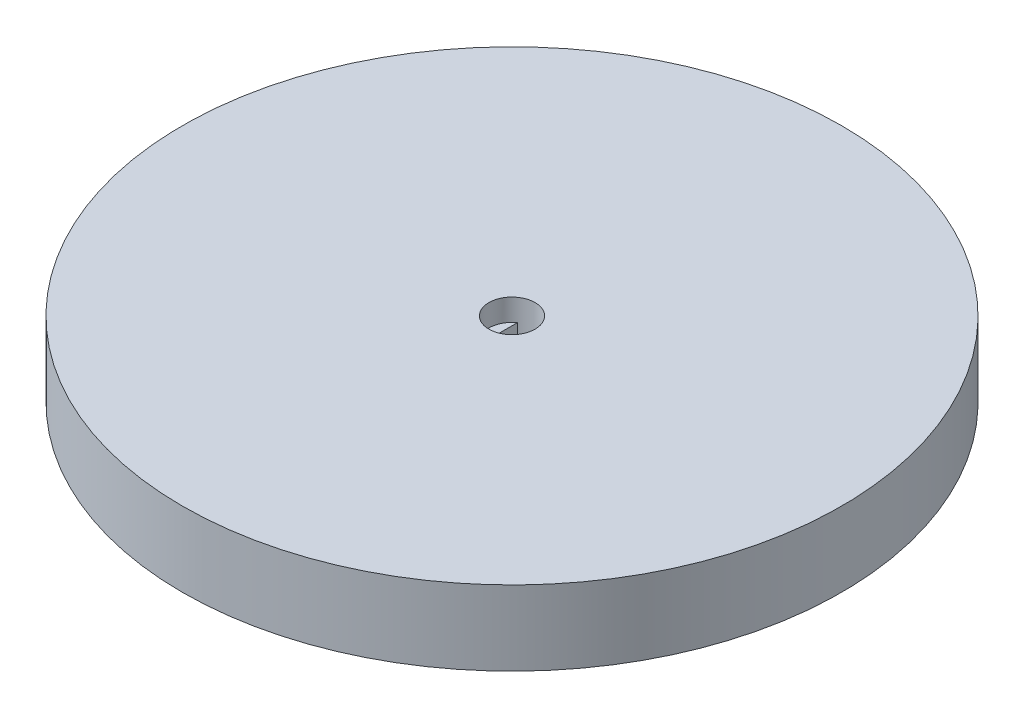
SolidWorks part; units mm, degrees
ref_plane "Front" through (0, 0, 0) normal (0, 0, 1) x (1, 0, 0)
ref_plane "Top" through (0, 0, 0) normal (0, 1, 0) x (1, 0, 0)
ref_plane "Right" through (0, 0, 0) normal (1, 0, 0) x (0, 0, -1)
sketch "Sketch1" plane through (0, 0, 0) normal (0, 1, 0) x (1, 0, 0)
  circle A0 centre (0, 0) radius 37.5
  dimension "D1" = 75
extrude "Boss-Extrude1" add sketch "Sketch1" along normal blind 8.5 contours A0
sketch "Sketch2" plane through (0, 8.5, 0) normal (0, 1, 0) x (1, 0, 0)
  circle A0 centre (0, 0) radius 2.625
  dimension "D1" = 5.25
extrude "Cut-Extrude1" cut sketch "Sketch2" against normal blind 2.5 contours A0
sketch "Sketch3" plane through (0, 6, 0) normal (0, 1, 0) x (1, 0, 0)
  line L0 (-1.525, 2.1366) -> (-1.525, -2.1366)
  line L1 (1.525, 2.1366) -> (1.525, -2.1366)
  line L2 (-1.525, 0) -> (1.525, 0) construction
  circle A0 centre (0, 0) radius 2.625 construction
  arc A1 (-1.525, 2.1366) -> (1.525, 2.1366) centre (0, 0) cw
  arc A2 (-1.525, -2.1366) -> (1.525, -2.1366) centre (0, 0) ccw
  dimension "D1" = 3.05
extrude "Cut-Extrude2" cut sketch "Sketch3" against normal blind 6 contours A2 L1 A1 L0
